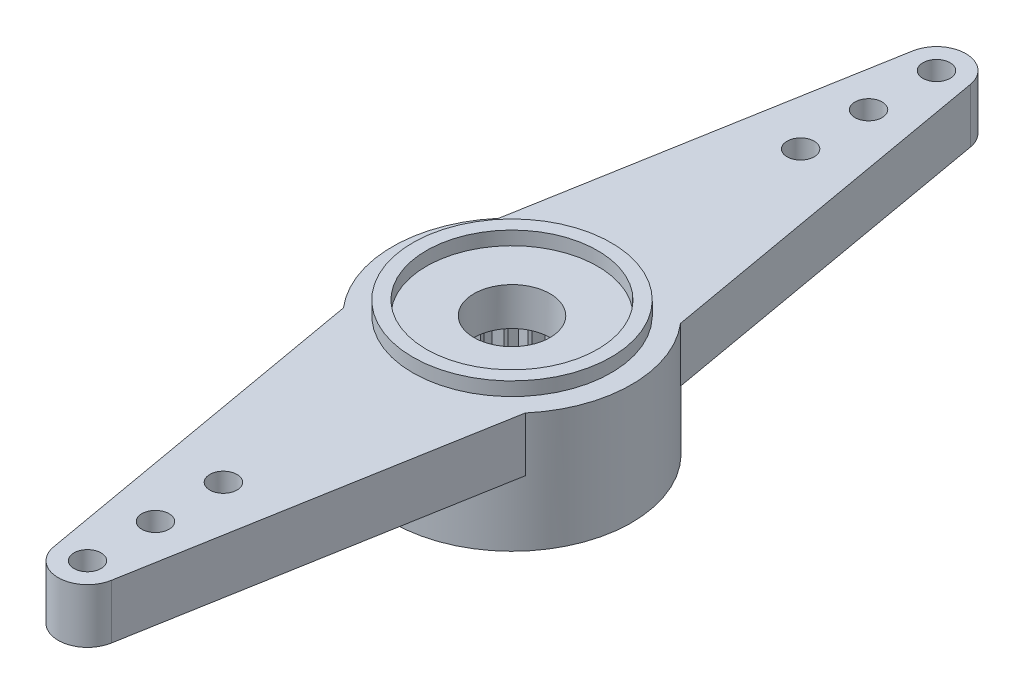
SolidWorks part; units mm, degrees
material "Polyethylene Cross-Linked"
ref_plane "Front Plane" through (0, 0, 0) normal (0, 0, 1) x (1, 0, 0)
ref_plane "Top Plane" through (0, 0, 0) normal (0, 1, 0) x (1, 0, 0)
ref_plane "Right Plane" through (0, 0, 0) normal (1, 0, 0) x (0, 0, -1)
sketch "BaseS" plane through (0, 0, 0) normal (0, 1, 0) x (1, 0, 0)
  circle A0 centre (0, 0) radius 4.4
  dimension "D1" = 8.8
extrude "BASE" add sketch "BaseS" along normal blind 4.4
sketch "TopBoreS" plane through (0, 4.4, 0) normal (0, 1, 0) x (1, 0, 0)
  circle A0 centre (0, 0) radius 1.4
  dimension "D1" = 2.8
extrude "TOP BORE" cut sketch "TopBoreS" against normal through all
sketch "HornHalfS" plane through (0, 4.4, 0) normal (0, 1, 0) x (1, 0, 0)
  line L0 (0, 0) -> (0, 15.62) construction
  line L1 (-1.0636, 15.8075) -> (-3.3473, 2.8557)
  line L2 (0, 16.7) -> (0, 15.62) construction
  line L3 (1.0636, 15.8075) -> (3.3473, 2.8557)
  arc A0 (1.0636, 15.8075) -> (-1.0636, 15.8075) centre (0, 15.62) ccw
  arc A1 (3.3473, 2.8557) -> (-3.3473, 2.8557) centre (0, 0) ccw
  circle A2 centre (0, 0) radius 4.4 construction
  dimension "D1" = 2.16
  dimension "D2" = 16.7
  dimension "D3" = 10
  dimension "D4" = 6.6947
extrude "HORN HALF" add sketch "HornHalfS" against normal blind 2
sketch "HornAttachS" plane through (0, 4.4, 0) normal (0, 1, 0) x (1, 0, 0)
  circle A0 centre (0, 15.62) radius 0.5
  dimension "D1" = 1
extrude "HORN ATTACH" cut sketch "HornAttachS" against normal through all
sketch "HA LP RS" plane through (0, 0, 0) normal (0, 1, 0) x (1, 0, 0)
  line L0 (0, 0) -> (0, 15.62) construction
pattern_linear "HA LP" count 3 spacing 2.5 along (0, 0, 1) of "HORN ATTACH"
mirror "HORN BODIES" about plane through (0, 0, 0) normal (0, 0, 1) of "HA LP", "HORN ATTACH", "HORN HALF"
sketch "ToothS" plane through (0, 0, 0) normal (0, -1, 0) x (1, 0, 0)
  line L0 (0, -2.9) -> (0.2629, -2.5867)
  line L1 (0, -2.9) -> (-0.2629, -2.5867)
  line L2 (0, -2.6) -> (0, -2.9) construction
  line L3 (0, 0) -> (0, -2.6) construction
  arc A0 (-0.2629, -2.5867) -> (0.2629, -2.5867) centre (0, 0) ccw
  dimension "D1" = 5.2
  dimension "D2" = 80
  dimension "D3" = 0.3
extrude "TOOTH" cut sketch "ToothS" against normal blind 3
pattern_circular "TOOTH CP" count 26 over 360 about axis through (0, 0, 0) along (0, 1, 0) of "TOOTH"
sketch "BottomBoreS" plane through (0, 0, 0) normal (0, -1, 0) x (-1, 0, 0)
  circle A0 centre (0, 0) radius 2.6
  arc A1 (0.2629, 2.5867) -> (-0.2629, 2.5867) centre (0, 0) ccw construction
extrude "BOTTOM BORE" cut sketch "BottomBoreS" against normal up to surface (3 mm away) up to face at (-0.6451, 3, 2.6172)
sketch "TopCutS" plane through (0, 4.4, 0) normal (0, 1, 0) x (1, 0, 0)
  circle A0 centre (0, 0) radius 3.65
  circle A1 centre (0, 0) radius 4.4 construction
  dimension "D1" = 0.75
  dimension "D2" = 7.3
sketch "TopPocketCylinderS" plane through (0, 4.4, 0) normal (0, 1, 0) x (1, 0, 0)
  circle A0 centre (0, 0) radius 3.15
  circle A1 centre (0, 0) radius 3.65
  arc A4 (3.3473, -2.8557) -> (3.3473, 2.8557) centre (0, 0) ccw construction
  dimension "D2" = 0.5
  dimension "D1" = 0.75
  dimension "D3" = 7.3
extrude "TOP POCKET CYLINDER" add sketch "TopPocketCylinderS" along normal offset from surface (0.5 mm away) 0.5 up to face at (0, 4.4, 12.62) offset beyond the face yes
